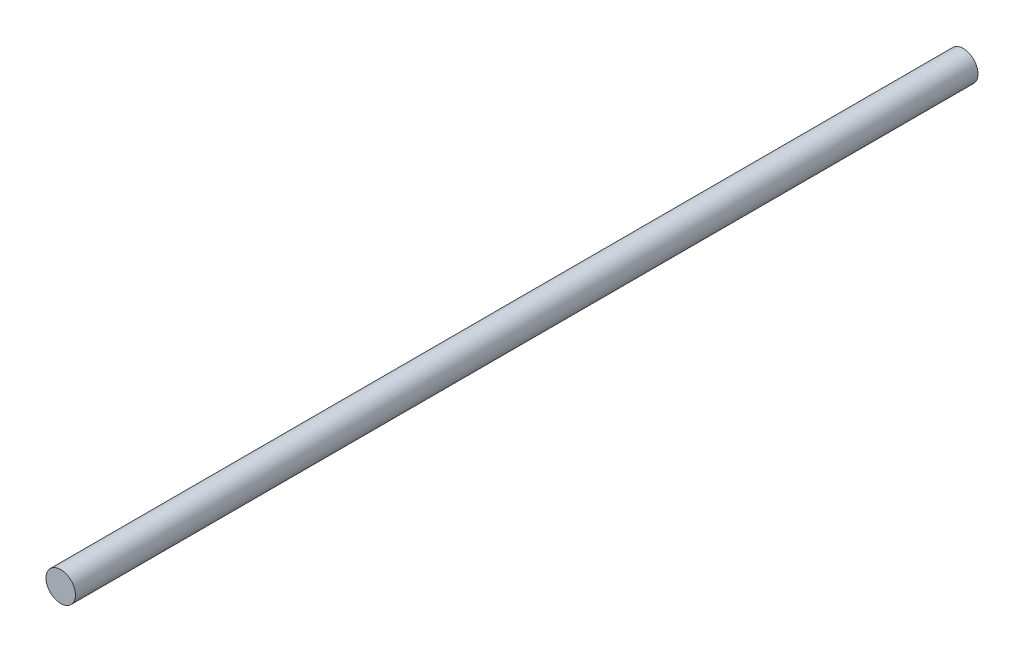
SolidWorks part; units mm, degrees
ref_plane "Front Plane" through (0, 0, 0) normal (0, 0, 1) x (1, 0, 0)
ref_plane "Top Plane" through (0, 0, 0) normal (0, 1, 0) x (1, 0, 0)
ref_plane "Right Plane" through (0, 0, 0) normal (1, 0, 0) x (0, 0, -1)
sketch "Sketch1" plane through (0, 0, 0) normal (0, 0, 1) x (1, 0, 0)
  circle A0 centre (0, 0) radius 3.937
  dimension "D1" = 7.874
extrude "Boss-Extrude1" add sketch "Sketch1" along normal blind 241.3
